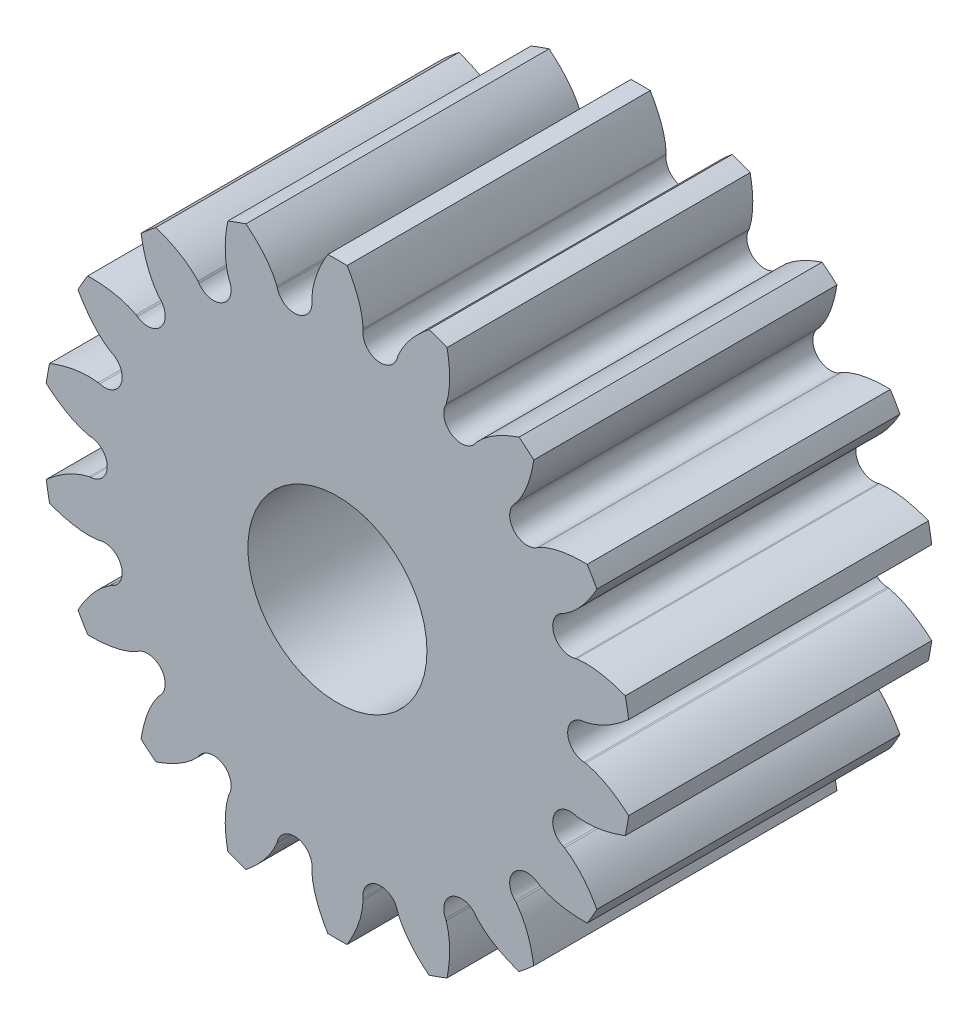
SolidWorks part; units mm, degrees
material "PE Low/Medium Density"
ref_plane "Front Plane" through (0, 0, 0) normal (0, 0, 1) x (1, 0, 0)
ref_plane "Top Plane" through (0, 0, 0) normal (0, 1, 0) x (1, 0, 0)
ref_plane "Right Plane" through (0, 0, 0) normal (1, 0, 0) x (0, 0, -1)
sketch "Involute construction sketch" plane through (0, 0, 0) normal (0, 0, 1) x (1, 0, 0)
  line L0 (0, 0) -> (-1.8157, 1.6751) construction
  line L1 (0, 0) -> (-1.2188, 2.1487) construction
  line L2 (0, 0) -> (-0.506, 2.418) construction
  line L3 (0, 0) -> (0.255, 2.4572) construction
  line L4 (-2.4509, 0.3098) -> (-2.2398, 1.042) construction
  line L5 (-2.2398, 1.042) -> (-1.8157, 1.6751) construction
  line L6 (-1.8157, 1.6751) -> (-1.2188, 2.1487) construction
  line L7 (0, 0) -> (-2.2398, 1.042) construction
  line L8 (0, 0) -> (-2.4509, 0.3098) construction
  line L9 (-1.2188, 2.1487) -> (-0.506, 2.418) construction
  line L10 (-0.506, 2.418) -> (0.255, 2.4572) construction
  line L11 (-2.4509, 0.3098) -> (-1.9731, 4.0897) construction
  line L12 (-2.2398, 1.042) -> (-0.9542, 3.8056) construction
  line L13 (-1.8157, 1.6751) -> (-0.2657, 3.3553) construction
  line L14 (-1.2188, 2.1487) -> (0.1068, 2.9007) construction
  line L15 (-0.506, 2.418) -> (0.2399, 2.5741) construction
  line L17 (0, 0) -> (0, 5.7859) construction
  line L18 (0, 0) -> (0.2291, 2.6189) construction
  line L19 (0, 0) -> (0.397, 2.2513) construction
  circle A0 centre (0, 0) radius 2.286 construction
  circle A1 centre (0, 0) radius 2.4704 construction
  circle A2 centre (0, 0) radius 2.6289 construction
  circle A3 centre (0, 0) radius 2.921 construction
  spline S0 degree 3 poles (0.255, 2.4572) (0.2476, 2.615) (0.11, 2.9502) (-0.5314, 3.7068) (-1.3595, 4.0133) (-1.9731, 4.0897) knots 0 0 0 0 0.160126 0.360107 1 1 1 1 construction
  point P17 (0.0957, 2.9194)
  dimension "D1" = 4.572
  dimension "D2" = 4.9407
  dimension "D3" = 5.2578
  dimension "D4" = 5.842
  dimension "D5" = 0.762
  dimension "D6" = 1.524
  dimension "D7" = 2.286
  dimension "D8" = 3.048
  dimension "D9" = 3.81
  dimension "D10" = 5
  dimension "D11" = 10
sketch "Sketch2" plane through (0, 0, 0) normal (0, 0, 1) x (1, 0, 0)
  line L0 (0, 2.921) -> (0, 2.286)
  line L1 (0, 0) -> (0, 5.7859) construction
  line L2 (0.255, 2.4572) -> (0.2534, 2.4415)
  line L3 (0, 0) -> (0.255, 2.4572) construction
  circle A0 centre (0, 0) radius 2.921 construction
  circle A1 centre (0, 0) radius 2.286 construction
  arc A2 (0, 2.921) -> (0.0957, 2.9194) centre (0, 0) cw
  arc A3 (0, 2.286) -> (0.397, 2.2513) centre (0, 0) cw
  arc A4 (0.2534, 2.4415) -> (0.397, 2.2513) centre (0.4273, 2.4235) ccw
  spline S0 degree 3 poles (0.255, 2.4572) (0.2525, 2.512) (0.2249, 2.6747) (0.152, 2.8255) (0.0957, 2.9194) knots 0 0 0 0 0.332628 1 1 1 1
sketch "Sketch3" plane through (0, 0, 0) normal (0, 0, 1) x (1, 0, 0)
  circle A0 centre (0, 0) radius 2.286
  circle A1 centre (0, 0) radius 0.889
  dimension "D1" = 4.572
  dimension "D2" = 1.778
extrude "Base" add sketch "Sketch3" along normal blind 3.0099
extrude "Half tooth" add sketch "Sketch2" along normal up to surface (3.0099 mm away) up to face at (2.286, 0, 3.0099)
ref_plane "Midplane of half tooth" through (0, 0, 0) normal (-1, 0, 0) x (0, 0, 1)
mirror "Mirror of half tooth" about plane through (0, 0, 0) normal (-1, 0, 0) of "Half tooth"
pattern_circular "Pattern of half tooth" count 18 over 360 about axis through (0, 0, 3.0099) along (0, 0, 1) of "Half tooth", "Mirror of half tooth"
equation "\"radtodeg\"= 180 / PI'radian to degree conversion [ ]"
equation "\"phi\"= 20'pressure angle [deg]"
equation "\"N\"= 18'number of teeth [teeth]"
equation "\"A\"= 0.230in'diameter of addendum circle [inch]"
equation "\"B\"= 0.18in'diameter of dedendum circle [inch]"
equation "\"P\"= ( \"N\" + 2 ) / \"A\"'diametral pitch [teeth/inch]"
equation "\"d\"= \"N\" / \"P\"'diameter of pitch circle [inch]"
equation "\"cp\"= PI / \"P\"'circular pitch [inch/teeth]"
equation "\"add\"= 1 / \"P\"'addendum [inch]"
equation "\"ded\"= - ( \"B\" - \"d\" ) / 2'dedendum [inch]"
equation "\"clear\"= \"ded\" - \"add\"'clearance [inch]"
equation "\"C\"= \"B\" + 2 * \"clear\"'diameter of clearance circle [inch]"
equation "\"h\"= \"add\" + \"ded\"'tooth height / whole depth [inch]"
equation "\"s\"= \"d\" * cos ( \"phi\" * 1 / \"radtodeg\" )'diameter of base circle [inch]"
equation "\"t\"= ( PI / 2 ) / \"P\"'tooth width at diameter of pitch circle diameter [inch]"
equation "\"alpha\"= ( \"t\" / ( \"d\" / 2 ) * \"radtodeg\" ) / 2'arc angle for half of tooth width at pitch circle diameter [inch]"
equation "\"bore\"= 0.07'bore of hub [inch]"
equation "\"D4@Involute construction sketch\"= \"A\"'addendum circle"
equation "\"D3@Involute construction sketch\"= \"d\"'pitch circle"
equation "\"D2@Involute construction sketch\"= \"s\"'base circle"
equation "\"D1@Involute construction sketch\"= \"B\"'dedendum circle"
equation "\"seg\"= \"D5@Involute construction sketch\"'size of one involute segment [inch]"
equation "\"D6@Involute construction sketch\"=2*\"seg\""
equation "\"D7@Involute construction sketch\"=3*\"seg\""
equation "\"D8@Involute construction sketch\"=4*\"seg\""
equation "\"D9@Involute construction sketch\"=5*\"seg\""
equation "\"D10@Involute construction sketch\"=\"alpha\""
equation "\"D11@Involute construction sketch\"=2*\"alpha\""
equation "\"D1@Sketch3\"=\"B\""
equation "\"D2@Sketch3\"=\"bore\""
